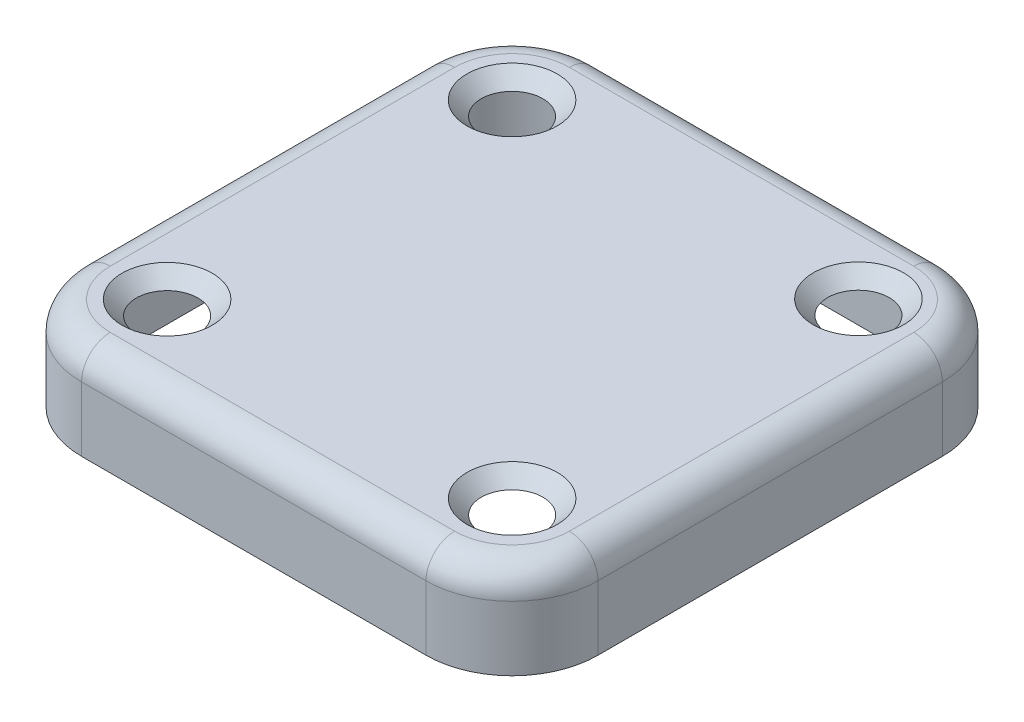
SolidWorks part; units mm, degrees
material "ABS"
ref_plane "Front Plane" through (0, 0, 0) normal (0, 0, 1) x (1, 0, 0)
ref_plane "Top Plane" through (0, 0, 0) normal (0, 1, 0) x (1, 0, 0)
ref_plane "Right Plane" through (0, 0, 0) normal (1, 0, 0) x (0, 0, -1)
sketch "Sketch5" plane through (0, 0, 0) normal (0, 1, 0) x (1, 0, 0)
  line L0 (-12.02, -12.02) -> (12.02, 12.02) construction
  line L5 (12.02, -12.02) -> (-12.02, -12.02) construction
  line L6 (12.02, -12.02) -> (12.02, 12.02) construction
  line L7 (12.02, 12.02) -> (-12.02, 12.02) construction
  line L8 (-12.02, -12.02) -> (-12.02, 12.02) construction
  line L9 (12.02, -12.02) -> (-12.02, 12.02) construction
  line L10 (12.02, 12.02) -> (-12.02, -12.02) construction
  line L11 (-16.2626, -7.7774) -> (7.7774, 16.2626)
  line L12 (-7.7774, -16.2626) -> (16.2626, 7.7774)
  line L13 (12.02, -12.02) -> (-12.02, 12.02) construction
  line L14 (7.7774, -16.2626) -> (-16.2626, 7.7774)
  line L15 (16.2626, -7.7774) -> (-7.7774, 16.2626)
  line L16 (12.02, 18.02) -> (-12.02, 18.02)
  line L17 (-18.02, 12.02) -> (-18.02, -12.02)
  line L18 (18.02, 12.02) -> (18.02, -12.02)
  line L19 (12.02, -18.02) -> (-12.02, -18.02)
  line L23 (-17.02, -8.5347) -> (-17.02, 8.5347)
  circle A0 centre (-12.02, 12.02) radius 1.55
  circle A1 centre (-12.02, -12.02) radius 1.55
  circle A2 centre (12.02, -12.02) radius 1.55
  circle A3 centre (12.02, 12.02) radius 1.55
  arc A4 (-16.2626, -7.7774) -> (-7.7774, -16.2626) centre (-12.02, -12.02) ccw
  arc A5 (16.2626, 7.7774) -> (7.7774, 16.2626) centre (12.02, 12.02) ccw
  arc A6 (7.7774, -16.2626) -> (16.2626, -7.7774) centre (12.02, -12.02) ccw
  arc A7 (-7.7774, 16.2626) -> (-16.2626, 7.7774) centre (-12.02, 12.02) ccw
  point P0 (0, 0)
  point P10 (0, 0)
  point P15 (0, 0)
  point P37 (12.02, -15.52)
  dimension "D1" = 3.1
  dimension "D2" = 24.04
  dimension "D3" = 12
  dimension "D7" = 1
extrude "Boss-Extrude1" add sketch "Sketch5" against normal blind 1
hole_wizard "CSK for M3 Countersunk Flat Head Screw3" positions "3DSketch6" profile "Sketch15" countersink size "M3" standard "ISO"
sketch3d "3DSketch6"
  point P0 (12.02, 0, -12.02)
  point P3 (12.02, 0, -12.02)
  point P5 (12.0622, 0, -12.1176)
  point P7 (12.0445, 0, 12.0344)
  point P9 (-12.0458, 0, -12.0512)
  point P11 (-12.0379, 0, 12.0339)
sketch "Sketch15" plane through (-12.0379, 0, 12.0339) normal (1, 0, 0) x (0, 0, 1)
  line L0 (0, 0) -> (0, 1.001)
  line L1 (0, 1.001) -> (1.7, 1.001)
  line L2 (1.7, 1.001) -> (1.7, 1.45)
  line L3 (1.7, 1.45) -> (3.15, 0)
  line L5 (3.15, 0) -> (0, 0)
  line L6 (-1.7, 1.45) -> (-3.15, 0) construction
  line L11 (0, -6.35) -> (0, 107.95) construction
  dimension "Thru Hole Dia." = 3.4
  dimension "Thru Hole Depth" = 1.001
  dimension "Near C'Sink Dia." = 6.3
  dimension "Near C'Sink Angle" = 90
sketch "Sketch16" plane through (0, -1, 0) normal (0, -1, 0) x (1, 0, 0)
  line L20 (17.02, -12.02) -> (17.02, 12.02)
  line L21 (-12.02, -17.02) -> (12.02, -17.02)
  line L22 (-17.02, 12.02) -> (-17.02, -12.02)
  line L23 (12.02, 17.02) -> (-12.02, 17.02)
  line L24 (17.02, -12.02) -> (17.02, 12.02)
  line L25 (-12.02, -17.02) -> (12.02, -17.02)
  line L26 (-17.02, 12.02) -> (-17.02, -12.02)
  line L27 (12.02, 17.02) -> (-12.02, 17.02)
  line L28 (18.02, -12.02) -> (18.02, 12.02)
  line L29 (12.02, 18.02) -> (-12.02, 18.02)
  line L30 (-18.02, 12.02) -> (-18.02, -12.02)
  line L31 (-12.02, -18.02) -> (12.02, -18.02)
  line L32 (18.02, -12.02) -> (18.02, 12.02)
  line L33 (12.02, 18.02) -> (-12.02, 18.02)
  line L34 (-18.02, 12.02) -> (-18.02, -12.02)
  line L35 (-12.02, -18.02) -> (12.02, -18.02)
  arc A24 (12.02, -17.02) -> (17.02, -12.02) centre (12.02, -12.02) ccw
  arc A25 (-17.02, -12.02) -> (-12.02, -17.02) centre (-12.02, -12.02) ccw
  arc A26 (-12.02, 17.02) -> (-17.02, 12.02) centre (-12.02, 12.02) ccw
  arc A27 (17.02, 12.02) -> (12.02, 17.02) centre (12.02, 12.02) ccw
  arc A28 (12.02, -17.02) -> (17.02, -12.02) centre (12.02, -12.02) ccw
  arc A29 (-17.02, -12.02) -> (-12.02, -17.02) centre (-12.02, -12.02) ccw
  arc A30 (-12.02, 17.02) -> (-17.02, 12.02) centre (-12.02, 12.02) ccw
  arc A31 (17.02, 12.02) -> (12.02, 17.02) centre (12.02, 12.02) ccw
  arc A32 (12.02, -18.02) -> (18.02, -12.02) centre (12.02, -12.02) ccw
  arc A33 (18.02, 12.02) -> (12.02, 18.02) centre (12.02, 12.02) ccw
  arc A34 (-12.02, 18.02) -> (-18.02, 12.02) centre (-12.02, 12.02) ccw
  arc A35 (-18.02, -12.02) -> (-12.02, -18.02) centre (-12.02, -12.02) ccw
  arc A36 (12.02, -18.02) -> (18.02, -12.02) centre (12.02, -12.02) ccw
  arc A37 (18.02, 12.02) -> (12.02, 18.02) centre (12.02, 12.02) ccw
  arc A38 (-12.02, 18.02) -> (-18.02, 12.02) centre (-12.02, 12.02) ccw
  arc A39 (-18.02, -12.02) -> (-12.02, -18.02) centre (-12.02, -12.02) ccw
  dimension "D1" = 1
  dimension "D2" = 0
extrude "Boss-Extrude3" add sketch "Sketch16" along normal blind 5.5 contours A36 L32 A37 L33 A38 L34 A39 L35 | L24 A31 L27 A30 L26 A29 L25 A28
fillet "Fillet1" radius 2 8 edges at (16.2626, 0, -16.2626) (0, 0, -18.02) (-16.2626, 0, -16.2626) (-18.02, 0, 0) (-16.2626, 0, 16.2626) (0, 0, 18.02) (16.2626, 0, 16.2626) (18.02, 0, 0)
fillet "Fillet2" radius 1 8 edges at (15.5555, -1, -15.5555) (0, -1, -17.02) (-15.5555, -1, -15.5555) (-17.02, -1, 0) (-15.5555, -1, 15.5555) (0, -1, 17.02) (15.5555, -1, 15.5555) (17.02, -1, 0)
